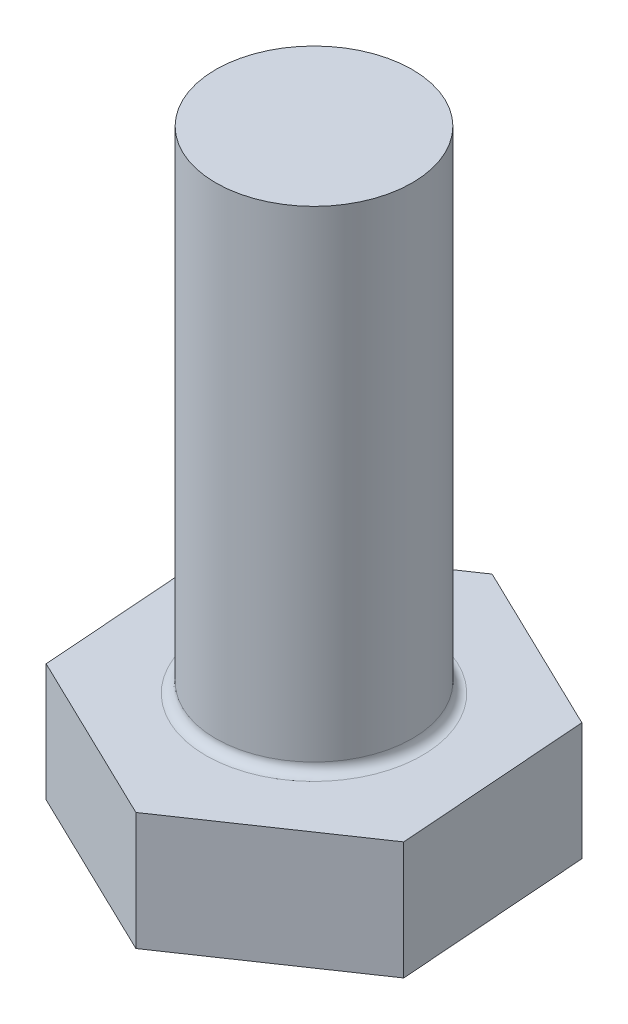
SolidWorks part; units mm, degrees
ref_plane "Płaszczyzna XY" through (0, 0, 0) normal (0, 0, 1) x (1, 0, 0)
ref_plane "Płaszczyzna XZ" through (0, 0, 0) normal (0, 1, 0) x (1, 0, 0)
ref_plane "Płaszczyzna YZ" through (0, 0, 0) normal (1, 0, 0) x (0, 0, -1)
sketch "Szkic1" plane through (0, 0, 0) normal (0, 1, 0) x (1, 0, 0)
  circle A0 centre (0, 0) radius 5
  dimension "D1" = 10
extrude "Dodanie-wyciągnięcie1" add sketch "Szkic1" along normal blind 25
sketch "Szkic2" plane through (0, 0, 0) normal (0, -1, 0) x (-1, 0, 0)
  line L1 (-0.7211, -9.7884) -> (8.1165, -5.5187)
  line L2 (8.1165, -5.5187) -> (8.8376, 4.2697)
  line L3 (8.8376, 4.2697) -> (0.7211, 9.7884)
  line L4 (0.7211, 9.7884) -> (-8.1165, 5.5187)
  line L5 (-8.1165, 5.5187) -> (-8.8376, -4.2697)
  line L6 (-8.8376, -4.2697) -> (-0.7211, -9.7884)
  circle A0 centre (0, 0) radius 8.5 construction
  dimension "D1" = 17
extrude "Dodanie-wyciągnięcie2" add sketch "Szkic2" along normal blind 6
fillet "Zaokrąglenie1" radius 0.5 1 edges at (0, 0, 5)
